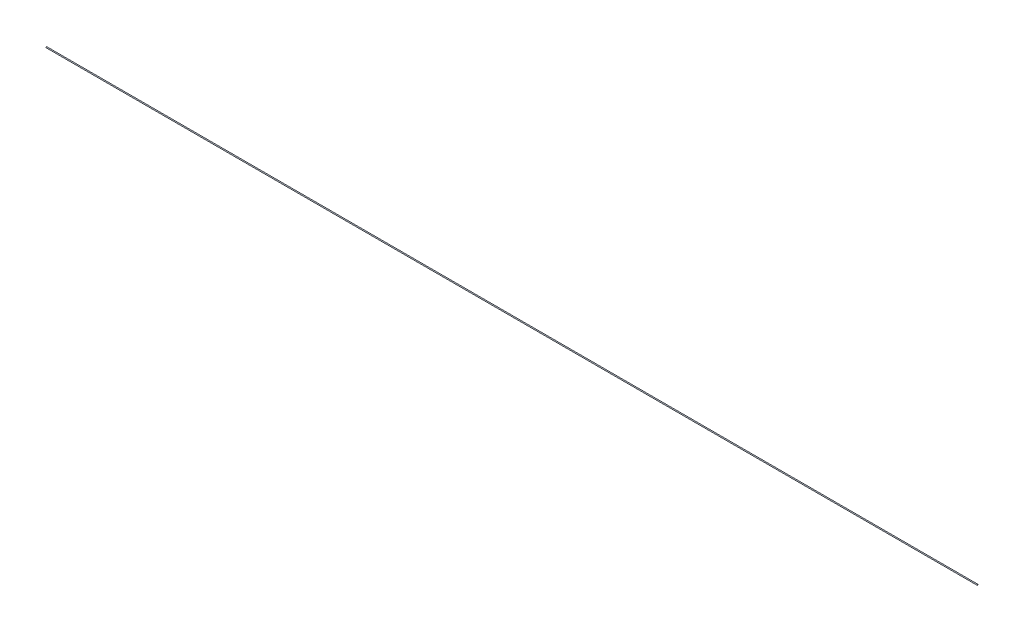
SolidWorks part; units mm, degrees
ref_plane "Front Plane" through (0, 0, 0) normal (0, 0, 1) x (1, 0, 0)
ref_plane "Top Plane" through (0, 0, 0) normal (0, 1, 0) x (1, 0, 0)
ref_plane "Right Plane" through (0, 0, 0) normal (1, 0, 0) x (0, 0, -1)
sketch "Sketch1" plane through (0, 0, 0) normal (1, 0, 0) x (0, 0, -1)
  circle A0 centre (0, 0) radius 0.127
  dimension "D1" = 0.254
extrude "Boss-Extrude1" add sketch "Sketch1" along normal blind 260
